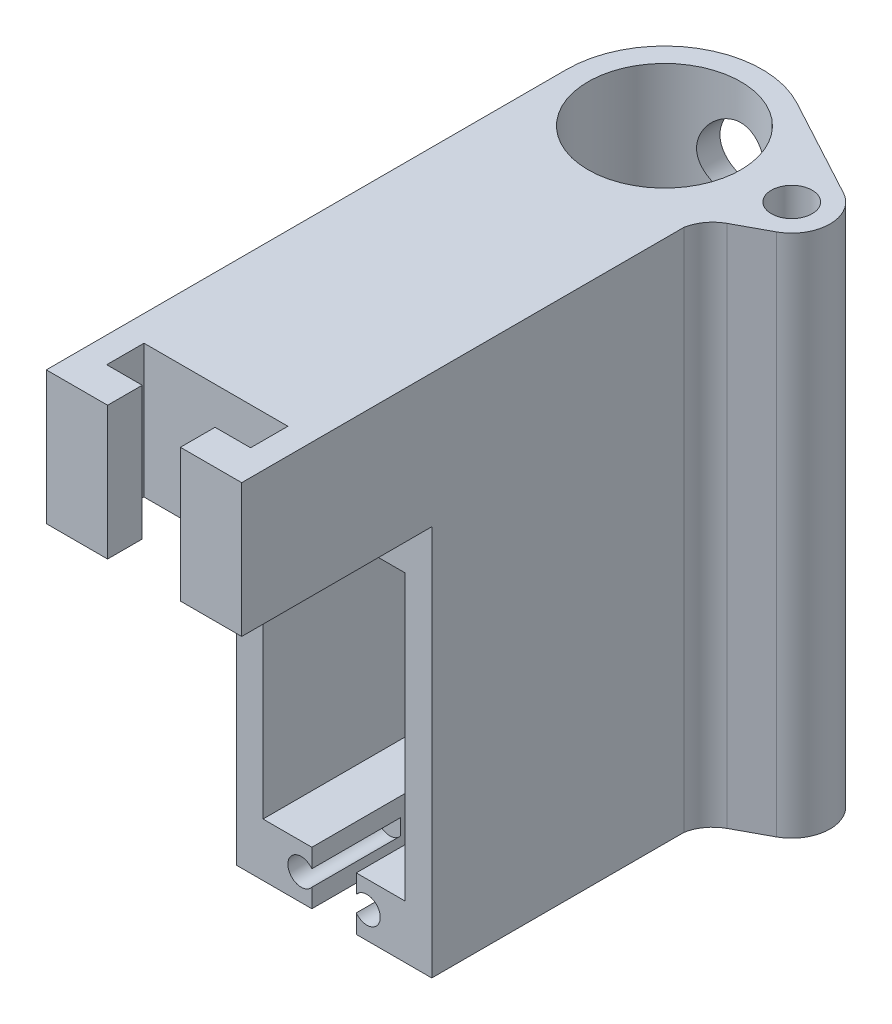
SolidWorks part; units mm, degrees
ref_plane "Front Plane" through (0, 0, 0) normal (0, 0, 1) x (1, 0, 0)
ref_plane "Top Plane" through (0, 0, 0) normal (0, 1, 0) x (1, 0, 0)
ref_plane "Right Plane" through (0, 0, 0) normal (1, 0, 0) x (0, 0, -1)
sketch "Sketch2" plane through (0, 0, 0) normal (0, 0, 1) x (1, 0, 0)
  line L0 (-4.699, 24.13) -> (4.699, 24.13)
  line L1 (-10.16, 20.32) -> (10.16, 20.32)
  line L2 (-10.16, 20.32) -> (-10.16, 27.94)
  line L3 (-10.16, 27.94) -> (10.16, 27.94)
  line L4 (10.16, 20.32) -> (10.16, 27.94)
  line L5 (-10.16, 20.32) -> (10.16, 27.94) construction
  line L6 (-10.16, 27.94) -> (10.16, 20.32) construction
  line L7 (55, 0) -> (-55, 0) construction
  line L8 (-10.16, -27.94) -> (10.16, -20.32) construction
  line L9 (-10.16, -20.32) -> (10.16, -27.94) construction
  line L10 (10.16, -20.32) -> (10.16, -27.94)
  line L11 (-10.16, -27.94) -> (10.16, -27.94)
  line L12 (-10.16, -20.32) -> (-10.16, -27.94)
  line L13 (-10.16, -20.32) -> (10.16, -20.32)
  line L14 (-4.699, -24.13) -> (4.699, -24.13)
  circle A0 centre (4.699, 24.13) radius 1.905
  circle A1 centre (-4.699, 24.13) radius 1.905
  circle A2 centre (-4.699, -24.13) radius 1.905
  circle A3 centre (4.699, -24.13) radius 1.905
  point P0 (0, 24.13)
  point P10 (0, 24.13)
  point P23 (0, -24.13)
  dimension "D5" = 3.81
  dimension "D1" = 20.32
  dimension "D2" = 7.62
  dimension "D3" = 20.32
  dimension "D4" = 9.398
extrude "Boss-Extrude1" add sketch "Sketch2" along normal blind 12.7
sketch "Sketch4" plane through (0, 0, 12.7) normal (0, 0, 1) x (1, 0, 0)
  line L0 (-10.16, -27.94) -> (10.16, -27.94) construction
  line L1 (-10.16, 27.94) -> (-13.97, 27.94)
  line L2 (-10.16, 27.94) -> (-10.16, -27.94)
  line L3 (-10.16, -27.94) -> (-13.97, -27.94)
  line L4 (-13.97, 27.94) -> (-13.97, -27.94)
  line L6 (10.16, 27.94) -> (13.97, 27.94)
  line L7 (10.16, 27.94) -> (10.16, -27.94)
  line L8 (10.16, -27.94) -> (13.97, -27.94)
  line L9 (13.97, 27.94) -> (13.97, -27.94)
  dimension "D1" = 3.81
  dimension "D2" = 3.81
extrude "Boss-Extrude2" add sketch "Sketch4" against normal blind 28.702
sketch "Sketch5" plane through (0, 0, -16.002) normal (0, 0, -1) x (-1, 0, 0)
  line L5 (-13.97, 27.94) -> (13.97, 27.94)
  line L6 (-13.97, 27.94) -> (-13.97, -27.94)
  line L7 (-13.97, -27.94) -> (13.97, -27.94)
  line L8 (13.97, 27.94) -> (13.97, -27.94)
extrude "Boss-Extrude3" add sketch "Sketch5" along normal blind 7.62
sketch "Sketch6" plane through (0, 27.94, 0) normal (0, 1, 0) x (1, 0, 0)
  line L1 (8.7104, 23.622) -> (13.97, 23.622)
  line L2 (-13.97, 34.544) -> (-13.97, 23.622)
  line L3 (13.97, 34.544) -> (13.97, 23.622)
  line L4 (-13.97, 23.622) -> (-8.7104, 23.622)
  circle A0 centre (0, 34.544) radius 10.922
  arc A1 (-8.7104, 23.622) -> (8.7104, 23.622) centre (0, 34.544) ccw
  circle A2 centre (0, 34.544) radius 13.97 construction
  arc A3 (13.97, 34.544) -> (-13.97, 34.544) centre (0, 34.544) ccw
  point P9 (0, 0)
  point P14 (0, 0)
  dimension "D1" = 21.844
  dimension "D2" = 3.048
extrude "Boss-Extrude6" add sketch "Sketch6" against normal up to surface (55.88 mm away) up to face at (0, -27.94, -8.001)
sketch "Sketch10" plane through (0, 27.94, 0) normal (0, 1, 0) x (1, 0, 0)
  line L1 (-10.16, 16.002) -> (10.16, 16.002)
  line L2 (-10.16, 16.002) -> (-10.16, 0)
  line L3 (-10.16, 0) -> (10.16, 0)
  line L4 (10.16, 16.002) -> (10.16, 0)
extrude "Boss-Extrude7" add sketch "Sketch10" against normal up to surface (7.62 mm away) up to face at (0, 20.32, 6.35)
sketch "Sketch11" plane through (0, -27.94, 0) normal (0, -1, 0) x (1, 0, 0)
  line L3 (13.97, -34.544) -> (13.97, 12.7)
  line L4 (13.97, 12.7) -> (-13.97, 12.7)
  line L5 (-13.97, 12.7) -> (-13.97, -34.544)
  line L6 (13.97, -34.544) -> (13.97, 12.7)
  line L7 (13.97, 12.7) -> (-13.97, 12.7)
  line L8 (-13.97, 12.7) -> (-13.97, -34.544)
  arc A1 (-13.97, -34.544) -> (13.97, -34.544) centre (0, -34.544) ccw
  arc A2 (-13.97, -34.544) -> (13.97, -34.544) centre (0, -34.544) ccw
  line M10 (10.16, -16.002) -> (-10.16, -16.002)
  line M11 (-10.16, -16.002) -> (-10.16, 0)
  line M12 (-10.16, 0) -> (10.16, 0)
  line M13 (10.16, 0) -> (10.16, -16.002)
  dimension "D1" = 0
extrude "Boss-Extrude8" add sketch "Sketch11" along direction (0, 1, 0) on the side against the normal up to surface (7.62 mm away) contours M10 M13 M12 M11
sketch "Sketch12" plane through (0, 27.94, 0) normal (0, 1, 0) x (1, 0, 0)
  line L0 (-13.97, 34.544) -> (-13.97, -12.7) construction
  line L1 (-13.97, -39.878) -> (13.97, -39.878)
  line L2 (-13.97, -39.878) -> (-13.97, 34.544)
  line L4 (13.97, -39.878) -> (13.97, 34.544)
  line L6 (-5.207, -34.925) -> (5.207, -34.925)
  line L7 (-5.207, -34.925) -> (-5.207, -39.878)
  line L8 (-13.97, 34.544) -> (-13.97, -12.7)
  line L9 (-13.97, -12.7) -> (13.97, -12.7)
  line L10 (13.97, -12.7) -> (13.97, 34.544)
  line L11 (-13.97, 34.544) -> (-13.97, -12.7)
  line L13 (13.97, -12.7) -> (13.97, 34.544)
  line L14 (-5.207, -39.878) -> (5.207, -39.878)
  line L15 (5.207, -34.925) -> (5.207, -39.878)
  line L16 (-5.207, -34.925) -> (5.207, -39.878) construction
  line L17 (-5.207, -39.878) -> (5.207, -34.925) construction
  line L18 (-10.287, -29.591) -> (10.287, -29.591)
  line L19 (-10.287, -29.591) -> (-10.287, -34.925)
  line L20 (-10.287, -34.925) -> (10.287, -34.925)
  line L21 (10.287, -29.591) -> (10.287, -34.925)
  line L22 (-10.287, -29.591) -> (10.287, -34.925) construction
  line L23 (-10.287, -34.925) -> (10.287, -29.591) construction
  circle A0 centre (0, 34.544) radius 10.922
  arc A1 (13.97, 34.544) -> (-13.97, 34.544) centre (0, 34.544) ccw
  arc A2 (13.97, 34.544) -> (-13.97, 34.544) centre (0, 34.544) ccw
  point P12 (0, -37.4015)
  point P18 (0, -32.258)
  circle M9 centre (0, 34.544) radius 10.922
  arc M10 (13.97, 34.544) -> (-13.97, 34.544) centre (0, 34.544) ccw
  line M11 (-13.97, 34.544) -> (-13.97, -12.7)
  line M12 (-13.97, -12.7) -> (13.97, -12.7)
  line M13 (13.97, -12.7) -> (13.97, 34.544)
  dimension "D1" = 74.422
  dimension "D3" = 5.334
  dimension "D4" = 4.953
  dimension "D5" = 20.574
  dimension "D6" = 10.414
  dimension "D2" = 0
extrude "Boss-Extrude9" add sketch "Sketch12" along normal blind 19.05 contours L18 L21 L20 L15 L1 L4 L2 L7 L19 M12 | M13 M10 M11 M12 M9
sketch "Sketch14" plane through (0, 46.99, 0) normal (0, 1, 0) x (1, 0, 0)
  line L0 (21.1329, 39.012) -> (6.6358, 46.8374)
  line L1 (18.5389, 34.2064) -> (23.9999, 34.2064) construction
  line L2 (21.1329, 29.4008) -> (16.5554, 26.9299)
  line L3 (13.97, -39.878) -> (13.97, 34.544) construction
  line L4 (13.97, 26.3972) -> (13.97, 34.544)
  line L5 (13.97, 26.3972) -> (13.97, 23.3665)
  circle A0 centre (18.5389, 34.2064) radius 2.921
  circle A1 centre (0, 34.544) radius 10.922 construction
  arc A2 (21.1329, 29.4008) -> (21.1329, 39.012) centre (18.5389, 34.2064) ccw
  arc A3 (13.97, 34.544) -> (-13.97, 34.544) centre (0, 34.544) ccw construction
  arc A4 (13.97, 34.544) -> (6.6358, 46.8374) centre (0, 34.544) ccw
  circle A5 centre (18.5389, 34.2064) radius 5.461 construction
  arc A6 (13.97, 23.3665) -> (16.5554, 26.9299) centre (18.9684, 22.4596) cw
  dimension "D1" = 18.542
  dimension "D2" = 5.842
  dimension "D4" = 5.08
  dimension "D3" = 2.54
extrude "Boss-Extrude10" add sketch "Sketch14" against normal up to surface (74.93 mm away) up to face at (0, -27.94, -45.466)
ref_plane "Plane1" through (0, 0, -48.514) normal (0, 0, -1) x (-1, 0, 0)
sketch "Sketch17" plane through (0, 0, -48.514) normal (0, 0, -1) x (-1, 0, 0)
  line L0 (10.922, 46.99) -> (-10.922, 46.99) construction
  line L1 (10.922, 46.99) -> (-10.922, 46.99)
  circle A0 centre (0, 36.83) radius 5.08
  point P2 (0, 46.99)
  dimension "D1" = 10.16
  dimension "D2" = 10.16
extrude "Cut-Extrude3" cut sketch "Sketch17" against normal blind 32.766 contours A0
sketch "Sketch18" plane through (0, 0, 12.7) normal (0, 0, 1) x (1, 0, 0)
  line L0 (-10.16, -20.32) -> (10.16, -20.32) construction
  line L1 (-3.175, -27.94) -> (3.175, -27.94)
  line L2 (-3.175, -27.94) -> (-3.175, -20.32)
  line L3 (-3.175, -20.32) -> (3.175, -20.32)
  line L4 (3.175, -27.94) -> (3.175, -20.32)
  line L5 (-3.175, -27.94) -> (3.175, -20.32) construction
  line L6 (-3.175, -20.32) -> (3.175, -27.94) construction
  line L7 (-13.97, -27.94) -> (13.97, -27.94) construction
  point P0 (0, -24.13)
  point P7 (0, 0)
  point P8 (0, 0)
  dimension "D1" = 6.35
extrude "Cut-Extrude4" cut sketch "Sketch18" against normal up to surface (28.702 mm away) up to face at (0, 0, -16.002)
